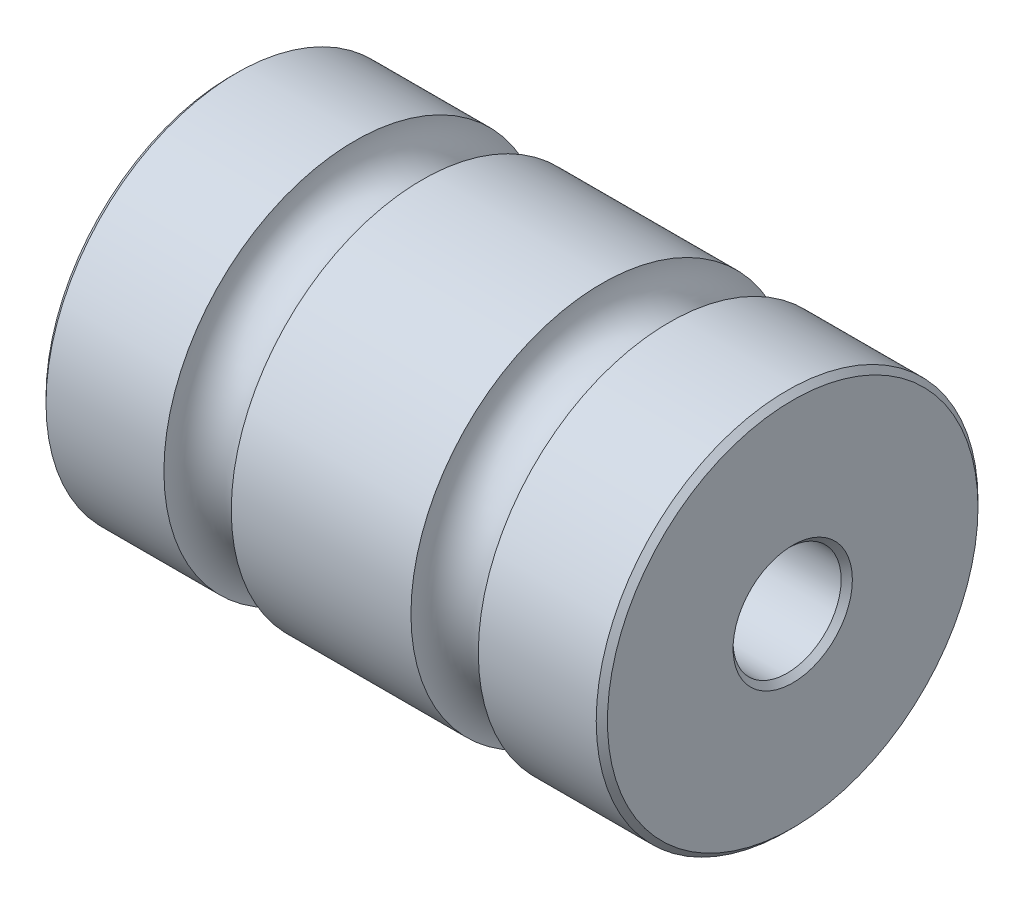
SolidWorks part; units mm, degrees
ref_plane "Front Plane" through (0, 0, 0) normal (0, 0, 1) x (1, 0, 0)
ref_plane "Top Plane" through (0, 0, 0) normal (0, 1, 0) x (1, 0, 0)
ref_plane "Right Plane" through (0, 0, 0) normal (1, 0, 0) x (0, 0, -1)
sketch "Sketch1" plane through (0, 0, 0) normal (0, 0, 1) x (1, 0, 0)
  line L0 (-25, 0) -> (25, 0)
  line L1 (25, 0) -> (25, -17)
  line L2 (25, -17) -> (14, -17)
  line L3 (8, -17) -> (-8, -17)
  line L5 (0, 0) -> (0, 8.8281) construction
  line L6 (-25, -17) -> (-14, -17)
  line L7 (-25, 0) -> (-25, -17)
  arc A0 (8, -17) -> (14, -17) centre (11, -17) cw
  arc A1 (-8, -17) -> (-14, -17) centre (-11, -17) ccw
  point P11 (0, -17)
  dimension "D1" = 3
  dimension "D2" = 11
  dimension "D3" = 25
  dimension "D4" = 17
revolve "Revolve1" add sketch "Sketch1" angle 360 about L0
sketch "Sketch2" plane through (25, 0, 0) normal (1, 0, 0) x (0, 0, -1)
  circle A0 centre (0, 18) radius 1.5
  circle A2 centre (0, 0) radius 17 construction
  dimension "D1" = 3
  dimension "D2" = 1
extrude "Cut-Extrude1" [suppressed] cut sketch "Sketch2" against normal through all
sketch "Sketch3" plane through (25, 0, 0) normal (1, 0, 0) x (0, 0, -1)
  circle A0 centre (0, 0) radius 4.8125
  dimension "D1" = 9.625
extrude "Cut-Extrude2" cut sketch "Sketch3" against normal through all
chamfer "Chamfer1" distance 0.5 angle 45 4 edges at (-25, 0, 17) (25, 0, 17) (-25, 0, -4.8125) (25, 0, -4.8125)
